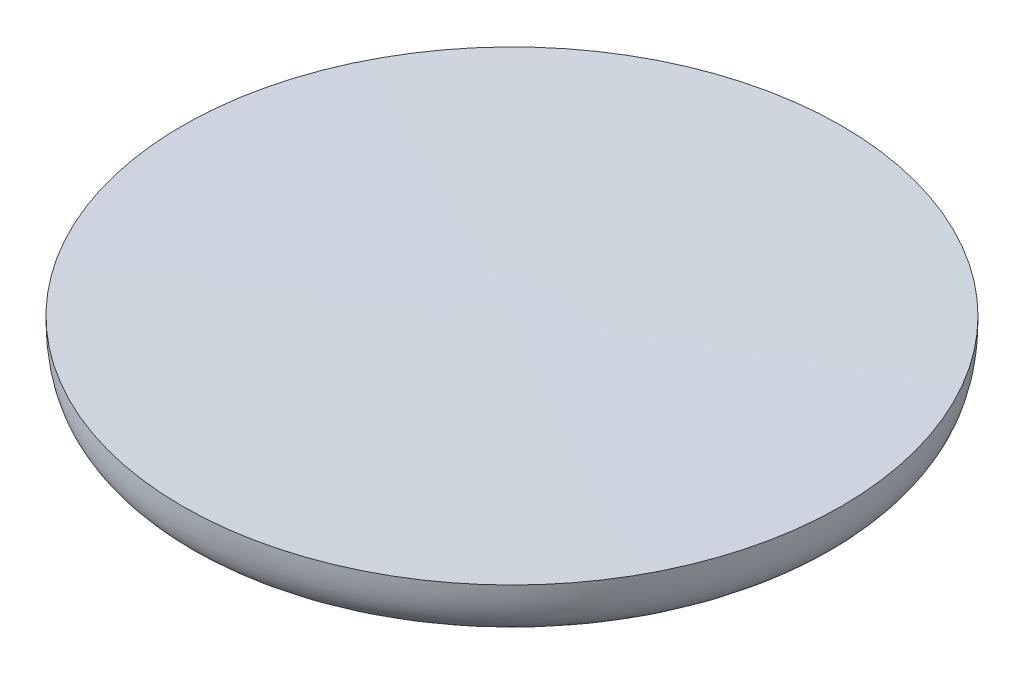
SolidWorks part; units mm, degrees
ref_plane "Front Plane" through (0, 0, 0) normal (0, 0, 1) x (1, 0, 0)
ref_plane "Top Plane" through (0, 0, 0) normal (0, 1, 0) x (1, 0, 0)
ref_plane "Right Plane" through (0, 0, 0) normal (1, 0, 0) x (0, 0, -1)
sketch "Sketch1" plane through (0, 0, 0) normal (0, 0, 1) x (1, 0, 0)
  line L0 (0, 0) -> (0, 24.0581)
  line L1 (124, 25) -> (0, 24.0581)
  spline S0 degree 3 poles (0, 0) (48.0418, 0.8795) (65.2974, -0.33) (120.0388, 3.9589) (124, 14.6373) (124, 25) knots 0 0 0 0 0.691992 0.8607 1 1 1 1
  dimension "D1" = 124
revolve "Revolve1" add sketch "Sketch1" angle 360 about L0
